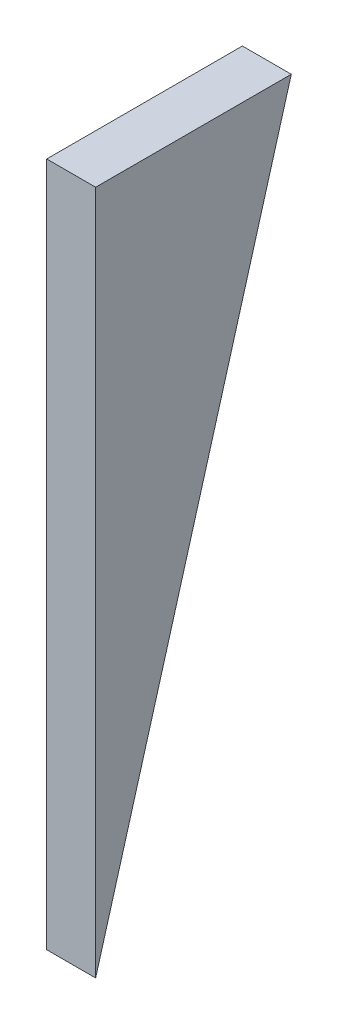
SolidWorks part; units mm, degrees
ref_plane "Front Plane" through (0, 0, 0) normal (0, 0, 1) x (1, 0, 0)
ref_plane "Top Plane" through (0, 0, 0) normal (0, 1, 0) x (1, 0, 0)
ref_plane "Right Plane" through (0, 0, 0) normal (1, 0, 0) x (0, 0, -1)
sketch3d "reference sketch"
  line L1 (0, 88.9, 0) -> (0, -88.9, 0)
  point P0 (0, 0, 0)
sketch3d "3DSketch2"
  line L0 (0, 88.9, 0) -> (0, -88.9, 0)
  point P4 (0, 0, 0)
  point P5 (0, 88.9, 0)
  point P6 (0, -88.9, 0)
  dimension "D1" = 177.8
sketch "Sketch1" plane through (0, 0, 0) normal (1, 0, 0) x (0, 0, -1)
  line L0 (0, 88.9) -> (50.8, 88.9)
  line L1 (50.8, 88.9) -> (0, -88.9)
  dimension "D1" = 50.8
ref_point "upper a - arm mounting point"
ref_point "lower a - arm mounting point"
ref_point "wheel mounting point"
sketch3d "3DSketch3"
  line L0 (-31.9032, 88.9, -50.8) -> (0, 88.9, -50.8)
  line L1 (0, 88.9, 0) -> (0, 88.9, -50.8) construction
  line L3 (0, 88.9, -50.8) -> (0, -88.9, 0) construction
sketch "Sketch2" plane through (0, 0, 0) normal (1, 0, 0) x (0, 0, -1)
  line L0 (0, 88.9) -> (50.8, 88.9) construction
  line L1 (0, 88.9) -> (0, -88.9) construction
  line L2 (50.8, 88.9) -> (0, -88.9) construction
  line L3 (0, 88.9) -> (50.8, 88.9)
  line L4 (0, 88.9) -> (0, -88.9)
  line L5 (50.8, 88.9) -> (0, -88.9)
extrude "Boss-Extrude1" add sketch "Sketch2" along normal mid plane 12.7
